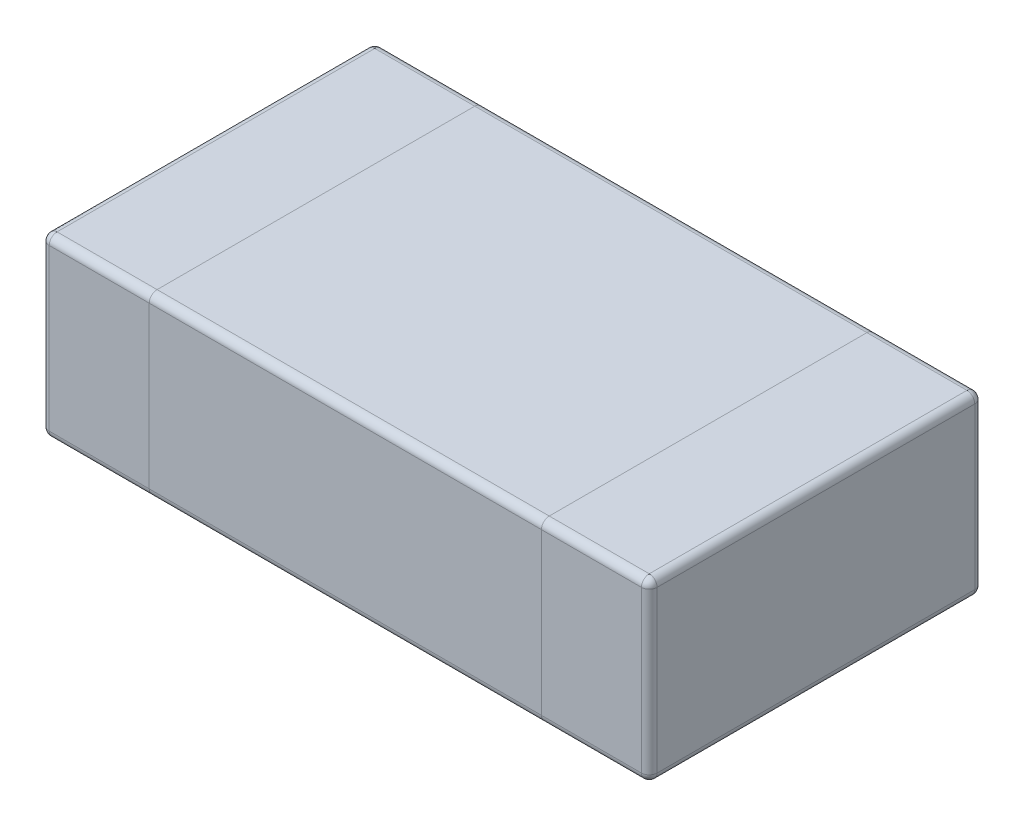
SolidWorks part; units mm, degrees
ref_plane "Front Plane" through (0, 0, 0) normal (0, 0, 1) x (1, 0, 0)
ref_plane "Top Plane" through (0, 0, 0) normal (0, 1, 0) x (1, 0, 0)
ref_plane "Right Plane" through (0, 0, 0) normal (1, 0, 0) x (0, 0, -1)
sketch "Sketch1" plane through (0, 0, 0) normal (0, 1, 0) x (1, 0, 0)
  line L1 (-0.755, -0.425) -> (0.755, -0.425)
  line L2 (-0.775, -0.405) -> (-0.775, 0.405)
  line L3 (-0.755, 0.425) -> (0.755, 0.425)
  line L4 (0.775, -0.405) -> (0.775, 0.405)
  line L5 (-0.775, -0.425) -> (0.775, 0.425) construction
  line L6 (-0.775, 0.425) -> (0.775, -0.425) construction
  arc A4 (-0.775, -0.405) -> (-0.755, -0.425) centre (-0.755, -0.405) ccw
  arc A5 (0.755, -0.425) -> (0.775, -0.405) centre (0.755, -0.405) ccw
  arc A6 (0.775, 0.405) -> (0.755, 0.425) centre (0.755, 0.405) ccw
  arc A7 (-0.755, 0.425) -> (-0.775, 0.405) centre (-0.755, 0.405) ccw
  point P0 (0, 0)
  dimension "D4" = 0.02
  dimension "D1" = 1.55
  dimension "D2" = 0.85
extrude "Boss-Extrude1" add sketch "Sketch1" along normal mid plane 0.45
sketch "Sketch3" plane through (0, 0.225, 0) normal (0, 1, 0) x (1, 0, 0)
  line L0 (-0.5, 0) -> (0.5, 0) construction
  line L1 (-0.5, -0.5133) -> (-0.5, 0.5133)
  line L2 (0.5, -0.5133) -> (0.5, 0.5133)
  line L3 (0, -0.145) -> (0, 0.145) construction
  line L6 (-0.5, -0.145) -> (0.5, -0.145) construction
  point P4 (0, 0)
  point P8 (-0.5, 0)
  point P11 (0.5, 0)
  point P14 (0, 0)
  point P17 (0, -0.145)
  dimension "D1" = 1
  dimension "D2" = 0.29
sketch "Sketch4" plane through (0, 0, 0.425) normal (0, 0, 1) x (1, 0, 0)
  line L0 (-0.5, 0.225) -> (-0.5, -0.5946)
  line L1 (0.5, 0.225) -> (0.5, -0.5946)
sketch "Sketch5" plane through (0, 0, -0.425) normal (0, 0, -1) x (-1, 0, 0)
  line L0 (-0.5, 0.225) -> (-0.5, -0.5946) construction
  line L1 (-0.5, 0.225) -> (-0.5, -0.5946)
  line L2 (0.5, 0.225) -> (0.5, -0.5946) construction
  line L3 (0.5, 0.225) -> (0.5, -0.5946)
sketch "Sketch6" plane through (0, -0.225, 0) normal (0, -1, 0) x (1, 0, 0)
  line L0 (0.5, 0.5133) -> (0.5, -0.5133) construction
  line L1 (-0.5, 0.5133) -> (-0.5, -0.5133) construction
  line L2 (0.5, 0.5133) -> (0.5, -0.5133)
  line L3 (-0.5, 0.5133) -> (-0.5, -0.5133)
split line "Split Line2"
split line "Split Line3"
split line "Split Line4"
split line "Split Line5"
fillet "Fillet2" radius 0.02 24 edges at (0.6275, -0.225, 0.425) (-0.6275, -0.225, 0.425) (0, -0.225, 0.425) (-0.7691, -0.225, 0.4191) (-0.775, -0.225, 0) (-0.7691, -0.225, -0.4191) (-0.6275, -0.225, -0.425) (0.6275, -0.225, -0.425) (0, -0.225, -0.425) (0.7691, -0.225, -0.4191) (0.775, -0.225, 0) (0.7691, -0.225, 0.4191) (-0.6275, 0.225, -0.425) (0, 0.225, -0.425) (0.6275, 0.225, -0.425) (0.7691, 0.225, -0.4191) (0.775, 0.225, 0) (0.7691, 0.225, 0.4191) (-0.6275, 0.225, 0.425) (0, 0.225, 0.425) (0.6275, 0.225, 0.425) (-0.7691, 0.225, 0.4191) (-0.775, 0.225, 0) (-0.7691, 0.225, -0.4191)
